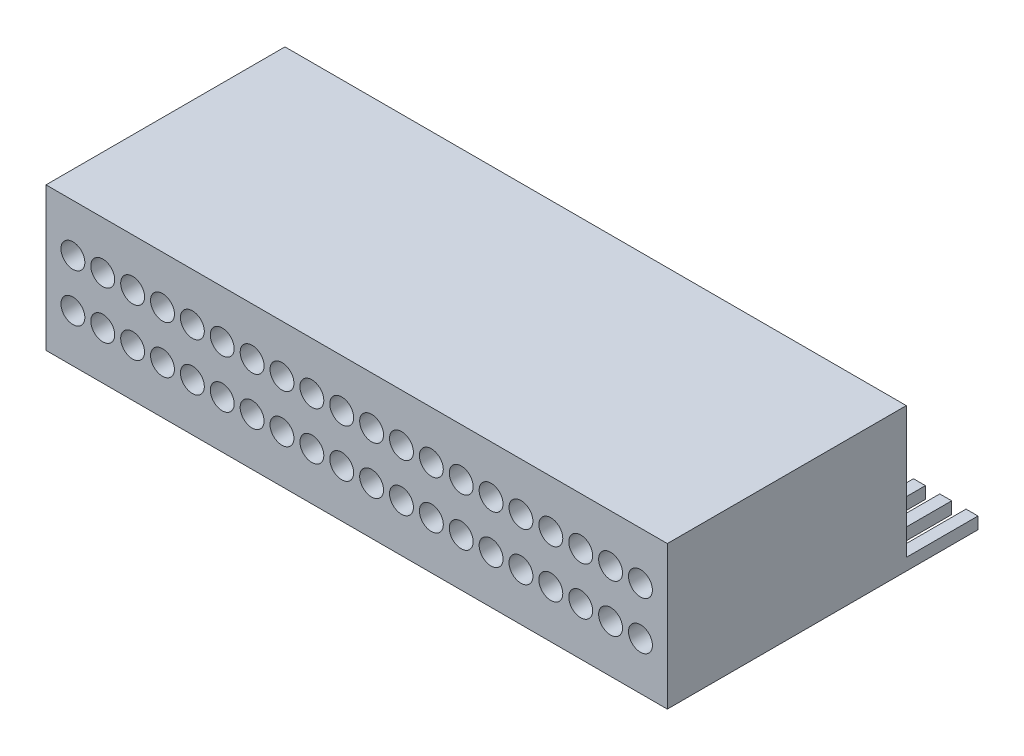
SolidWorks part; units mm, degrees
ref_plane "Front Plane" through (0, 0, 0) normal (0, 0, 1) x (1, 0, 0)
ref_plane "Top Plane" through (0, 0, 0) normal (0, 1, 0) x (1, 0, 0)
ref_plane "Right Plane" through (0, 0, 0) normal (1, 0, 0) x (0, 0, -1)
sketch "Sketch2" plane through (0, 0, 0) normal (0, 0, 1) x (1, 0, 0)
  line L1 (0, 0) -> (26, 0)
  line L2 (0, 0) -> (0, 6)
  line L3 (0, 6) -> (26, 6)
  line L4 (26, 0) -> (26, 6)
  dimension "D1" = 26
  dimension "D2" = 6
extrude "Boss-Extrude1" add sketch "Sketch2" along normal blind 10
sketch "Sketch3" plane through (0, 0, 10) normal (0, 0, 1) x (1, 0, 0)
  line L0 (0, 2) -> (26, 2) construction
  line L1 (0, 6) -> (0, 0) construction
  line L2 (26, 0) -> (26, 6) construction
  line L3 (0, 3) -> (26, 3) construction
  line L4 (26, 6) -> (0, 6) construction
  line L5 (0, 0) -> (26, 0) construction
  line L6 (1.125, 6) -> (1.125, 0) construction
  circle A0 centre (1.125, 2) radius 0.5
  circle A1 centre (2.375, 2) radius 0.5
  circle A2 centre (3.625, 2) radius 0.5
  circle A3 centre (4.875, 2) radius 0.5
  circle A4 centre (6.125, 2) radius 0.5
  circle A5 centre (7.375, 2) radius 0.5
  circle A6 centre (8.625, 2) radius 0.5
  circle A7 centre (9.875, 2) radius 0.5
  circle A8 centre (11.125, 2) radius 0.5
  circle A9 centre (12.375, 2) radius 0.5
  circle A10 centre (13.625, 2) radius 0.5
  circle A11 centre (14.875, 2) radius 0.5
  circle A12 centre (16.125, 2) radius 0.5
  circle A13 centre (17.375, 2) radius 0.5
  circle A14 centre (18.625, 2) radius 0.5
  circle A15 centre (19.875, 2) radius 0.5
  circle A16 centre (21.125, 2) radius 0.5
  circle A17 centre (22.375, 2) radius 0.5
  circle A18 centre (23.625, 2) radius 0.5
  circle A19 centre (24.875, 2) radius 0.5
  point P17 (2.3358, 2)
  point P55 (0, 0)
  dimension "D1" = 1
  dimension "D2" = 2
  dimension "D3" = 1.125
  dimension "D5" = 1.25
  dimension "D4" = 20
extrude "Cut-Extrude1" cut sketch "Sketch3" against normal blind 5
sketch "Sketch4" plane through (0, 0, 0) normal (0, -1, 0) x (-1, 0, 0)
  line L0 (-24.9, 0) -> (-24.9, 3)
  line L1 (-26, 0) -> (-25.5, 0)
  line L2 (-26, 0) -> (-26, 3)
  line L3 (-26, 3) -> (-25.5, 3)
  line L4 (-25.5, 0) -> (-25.5, 3)
  line L5 (-24.9, 3) -> (-24.4, 3)
  line L6 (-24.4, 0) -> (-24.4, 3)
  line L7 (-24.9, 0) -> (-24.4, 0)
  line L8 (-23.8, 0) -> (-23.8, 3)
  line L9 (-23.8, 3) -> (-23.3, 3)
  line L10 (-23.3, 0) -> (-23.3, 3)
  line L11 (-23.8, 0) -> (-23.3, 0)
  line L12 (-22.7, 0) -> (-22.7, 3)
  line L13 (-22.7, 3) -> (-22.2, 3)
  line L14 (-22.2, 0) -> (-22.2, 3)
  line L15 (-22.7, 0) -> (-22.2, 0)
  line L16 (-21.6, 0) -> (-21.6, 3)
  line L17 (-21.6, 3) -> (-21.1, 3)
  line L18 (-21.1, 0) -> (-21.1, 3)
  line L19 (-21.6, 0) -> (-21.1, 0)
  line L20 (-20.5, 0) -> (-20.5, 3)
  line L21 (-20.5, 3) -> (-20, 3)
  line L22 (-20, 0) -> (-20, 3)
  line L23 (-20.5, 0) -> (-20, 0)
  line L24 (-19.4, 0) -> (-19.4, 3)
  line L25 (-19.4, 3) -> (-18.9, 3)
  line L26 (-18.9, 0) -> (-18.9, 3)
  line L27 (-19.4, 0) -> (-18.9, 0)
  line L28 (-18.3, 0) -> (-18.3, 3)
  line L29 (-18.3, 3) -> (-17.8, 3)
  line L30 (-17.8, 0) -> (-17.8, 3)
  line L31 (-18.3, 0) -> (-17.8, 0)
  line L32 (-17.2, 0) -> (-17.2, 3)
  line L33 (-17.2, 3) -> (-16.7, 3)
  line L34 (-16.7, 0) -> (-16.7, 3)
  line L35 (-17.2, 0) -> (-16.7, 0)
  line L36 (-16.1, 0) -> (-16.1, 3)
  line L37 (-16.1, 3) -> (-15.6, 3)
  line L38 (-15.6, 0) -> (-15.6, 3)
  line L39 (-16.1, 0) -> (-15.6, 0)
  line L40 (-15, 0) -> (-15, 3)
  line L41 (-15, 3) -> (-14.5, 3)
  line L42 (-14.5, 0) -> (-14.5, 3)
  line L43 (-15, 0) -> (-14.5, 0)
  line L44 (-13.9, 0) -> (-13.9, 3)
  line L45 (-13.9, 3) -> (-13.4, 3)
  line L46 (-13.4, 0) -> (-13.4, 3)
  line L47 (-13.9, 0) -> (-13.4, 0)
  line L48 (-12.8, 0) -> (-12.8, 3)
  line L49 (-12.8, 3) -> (-12.3, 3)
  line L50 (-12.3, 0) -> (-12.3, 3)
  line L51 (-12.8, 0) -> (-12.3, 0)
  line L52 (-11.7, 0) -> (-11.7, 3)
  line L53 (-11.7, 3) -> (-11.2, 3)
  line L54 (-11.2, 0) -> (-11.2, 3)
  line L55 (-11.7, 0) -> (-11.2, 0)
  line L56 (-10.6, 0) -> (-10.6, 3)
  line L57 (-10.6, 3) -> (-10.1, 3)
  line L58 (-10.1, 0) -> (-10.1, 3)
  line L59 (-10.6, 0) -> (-10.1, 0)
  line L60 (-9.5, 0) -> (-9.5, 3)
  line L61 (-9.5, 3) -> (-9, 3)
  line L62 (-9, 0) -> (-9, 3)
  line L63 (-9.5, 0) -> (-9, 0)
  line L64 (-8.4, 0) -> (-8.4, 3)
  line L65 (-8.4, 3) -> (-7.9, 3)
  line L66 (-7.9, 0) -> (-7.9, 3)
  line L67 (-8.4, 0) -> (-7.9, 0)
  line L68 (-7.3, 0) -> (-7.3, 3)
  line L69 (-7.3, 3) -> (-6.8, 3)
  line L70 (-6.8, 0) -> (-6.8, 3)
  line L71 (-7.3, 0) -> (-6.8, 0)
  line L72 (-6.2, 0) -> (-6.2, 3)
  line L73 (-6.2, 3) -> (-5.7, 3)
  line L74 (-5.7, 0) -> (-5.7, 3)
  line L75 (-6.2, 0) -> (-5.7, 0)
  line L76 (-5.1, 0) -> (-5.1, 3)
  line L77 (-5.1, 3) -> (-4.6, 3)
  line L78 (-4.6, 0) -> (-4.6, 3)
  line L79 (-5.1, 0) -> (-4.6, 0)
  line L80 (-4, 0) -> (-4, 3)
  line L81 (-4, 3) -> (-3.5, 3)
  line L82 (-3.5, 0) -> (-3.5, 3)
  line L83 (-4, 0) -> (-3.5, 0)
  line L84 (-2.9, 0) -> (-2.9, 3)
  line L85 (-2.9, 3) -> (-2.4, 3)
  line L86 (-2.4, 0) -> (-2.4, 3)
  line L87 (-2.9, 0) -> (-2.4, 0)
  line L88 (-1.8, 0) -> (-1.8, 3)
  line L89 (-1.8, 3) -> (-1.3, 3)
  line L90 (-1.3, 0) -> (-1.3, 3)
  line L91 (-1.8, 0) -> (-1.3, 0)
  line L92 (-0.7, 0) -> (-0.7, 3)
  line L93 (-0.7, 3) -> (-0.2, 3)
  line L94 (-0.2, 0) -> (-0.2, 3)
  line L95 (-0.7, 0) -> (-0.2, 0)
  line L96 (-26, 0) -> (-24.9, 0) construction
  dimension "D1" = 3
  dimension "D2" = 0.5
  dimension "D4" = 1.1
  dimension "D3" = 24
extrude "Boss-Extrude2" add sketch "Sketch4" against normal blind 0.5
ref_plane "Plane1" through (0, 3, 0) normal (0, -1, 0) x (-1, 0, 0)
mirror "Mirror1" about plane through (0, 3, 0) normal (0, -1, 0) of "Cut-Extrude1"
sketch "Sketch5" plane through (0, 0, 10) normal (0, 0, 1) x (1, 0, 0)
  point P0 (1.125, 4)
  point P1 (2.375, 4)
  point P3 (3.625, 4)
  point P5 (4.875, 4)
  point P7 (6.125, 4)
  point P9 (7.375, 4)
  point P11 (8.625, 4)
  point P13 (9.875, 4)
  point P15 (11.125, 4)
  point P17 (12.375, 4)
  point P19 (13.625, 4)
  point P21 (14.875, 4)
  point P23 (16.125, 4)
  point P25 (17.375, 4)
  point P27 (18.625, 4)
  point P29 (19.875, 4)
  point P31 (21.125, 4)
  point P33 (22.375, 4)
  point P35 (23.625, 4)
  point P37 (24.875, 4)
  point P39 (24.875, 2)
  point P41 (23.625, 2)
  point P43 (22.375, 2)
  point P45 (21.125, 2)
  point P47 (19.875, 2)
  point P49 (18.625, 2)
  point P51 (17.375, 2)
  point P53 (16.125, 2)
  point P55 (14.875, 2)
  point P57 (13.625, 2)
  point P59 (12.375, 2)
  point P61 (11.125, 2)
  point P63 (9.875, 2)
  point P65 (8.625, 2)
  point P67 (7.375, 2)
  point P69 (6.125, 2)
  point P71 (4.875, 2)
  point P73 (3.625, 2)
  point P75 (2.375, 2)
  point P77 (1.125, 2)
